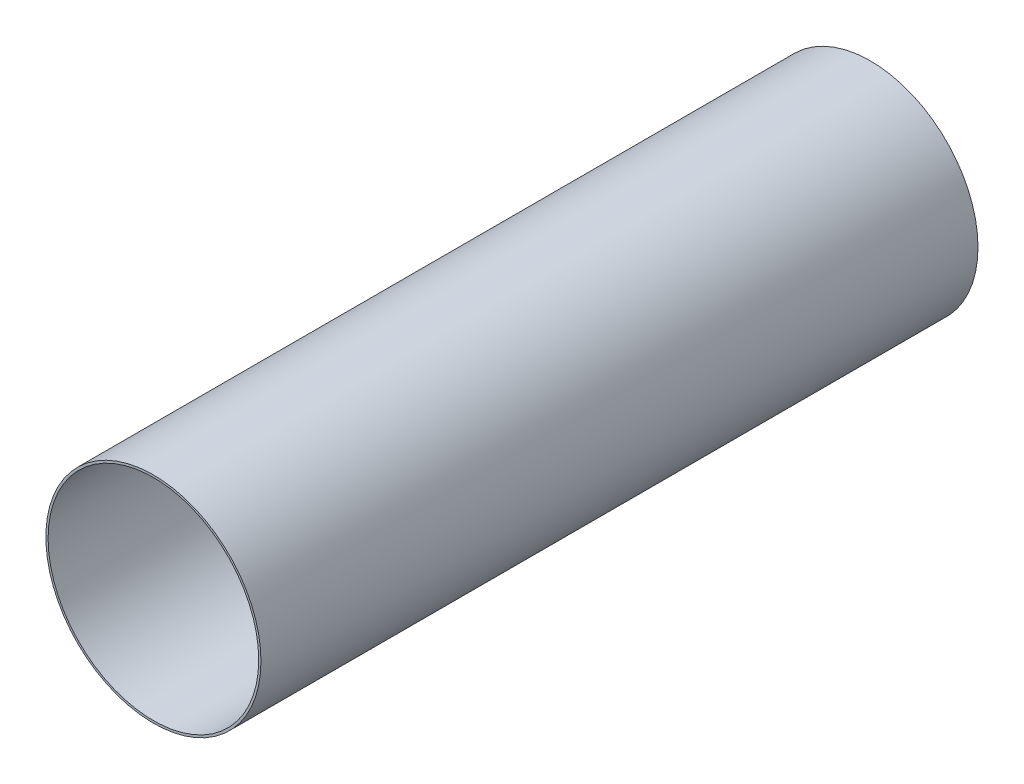
SolidWorks part; units mm, degrees
material "6061-T6 (SS)"
ref_plane "Front Plane" through (0, 0, 0) normal (0, 0, 1) x (1, 0, 0)
ref_plane "Top Plane" through (0, 0, 0) normal (0, 1, 0) x (1, 0, 0)
ref_plane "Right Plane" through (0, 0, 0) normal (1, 0, 0) x (0, 0, -1)
sketch "Sketch1" plane through (0, 0, 0) normal (0, 0, 1) x (1, 0, 0)
  circle A0 centre (0, 0) radius 152.4
  dimension "D1" = 304.8
extrude "Boss-Extrude1" add sketch "Sketch1" along normal blind 1016 contours A0
sketch "Sketch2" plane through (0, 0, 1016) normal (0, 0, 1) x (1, 0, 0)
  circle A0 centre (0, 0) radius 149.225
  dimension "D1" = 298.45
extrude "Cut-Extrude1" cut sketch "Sketch2" against normal blind 1016 contours A0
sketch "Sketch3" plane through (0, 0, 0) normal (0, 1, 0) x (1, 0, 0)
  line L0 (0, 0) -> (0, -25.4) construction
  circle A0 centre (0, -25.4) radius 3.175
  dimension "D1" = 6.35
extrude "Cut-Extrude2" [suppressed] cut sketch "Sketch3" along normal blind 190.5 contours A0
pattern_circular "CirPattern3" [suppressed] count 8 over 360
equation "\"Rocket Diameter\"= 12in"
equation "\"D1@Sketch1\"=\"Rocket Diameter\""
equation "\"Airframe Thickness\"= 0.125in"
equation "\"Length\"= 40in"
equation "\"D1@Boss-Extrude1\"=\"Length\""
equation "\"D1@Cut-Extrude1\"=\"Length\""
equation "\"Bolt Diameter\"= 0.25in"
equation "\"D1@Sketch3\"=\"Bolt Diameter\""
equation "\"D1@Sketch2\"= \"Rocket Diameter\"-\"Airframe Thickness\"*2"
